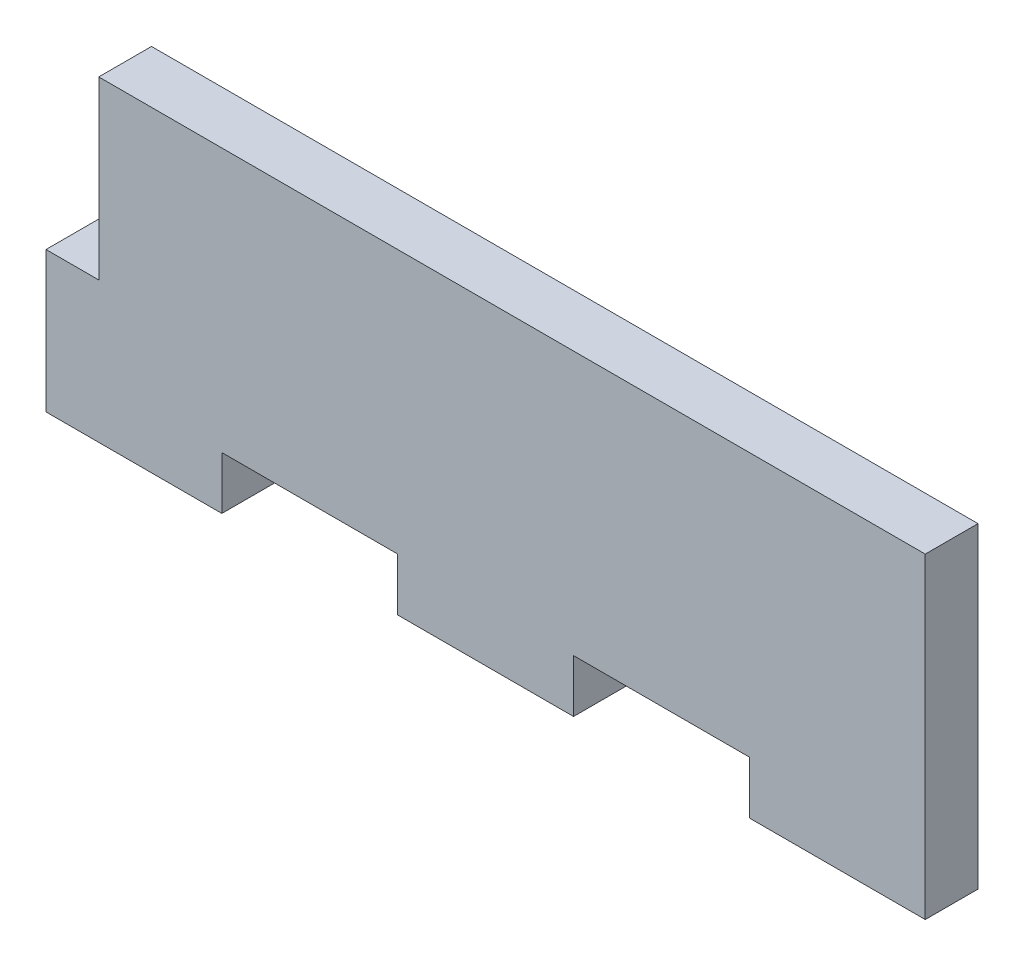
SolidWorks part; units mm, degrees
ref_plane "Plan de face" through (0, 0, 0) normal (0, 0, 1) x (1, 0, 0)
ref_plane "Plan de dessus" through (0, 0, 0) normal (0, 1, 0) x (1, 0, 0)
ref_plane "Plan de droite" through (0, 0, 0) normal (1, 0, 0) x (0, 0, -1)
sketch "Esquisse1" plane through (0, 0, 0) normal (0, 0, 1) x (1, 0, 0)
  line L1 (0, 0) -> (50, 0)
  line L2 (0, 0) -> (0, -18)
  line L3 (0, -18) -> (50, -18)
  line L4 (50, 0) -> (50, -18)
  dimension "D1" = 18
  dimension "D2" = 50
extrude "Boss.-Extru.1" add sketch "Esquisse1" along normal blind 3
sketch "Esquisse2" plane through (0, 0, 3) normal (0, 0, 1) x (1, 0, 0)
  line L0 (0, -18) -> (50, -18) construction
  line L1 (40, -18) -> (30, -18)
  line L2 (40, -18) -> (40, -15)
  line L3 (40, -15) -> (30, -15)
  line L4 (30, -18) -> (30, -15)
  line L5 (50, -18) -> (50, 0) construction
  dimension "D1" = 10
  dimension "D2" = 3
  dimension "D3" = 10
extrude "Enlèv. mat.-Extru.1" cut sketch "Esquisse2" against normal blind 3
pattern_linear "Répétition linéaire1" count 2 spacing 20 along (-1, 0, 0) of "Enlèv. mat.-Extru.1"
sketch "Esquisse3" plane through (0, 0, 3) normal (0, 0, 1) x (1, 0, 0)
  line L1 (0, 0) -> (3, 0)
  line L2 (0, 0) -> (0, -10)
  line L3 (0, -10) -> (3, -10)
  line L4 (3, 0) -> (3, -10)
  dimension "D1" = 3
  dimension "D2" = 10
extrude "Enlèv. mat.-Extru.2" cut sketch "Esquisse3" against normal blind 3
